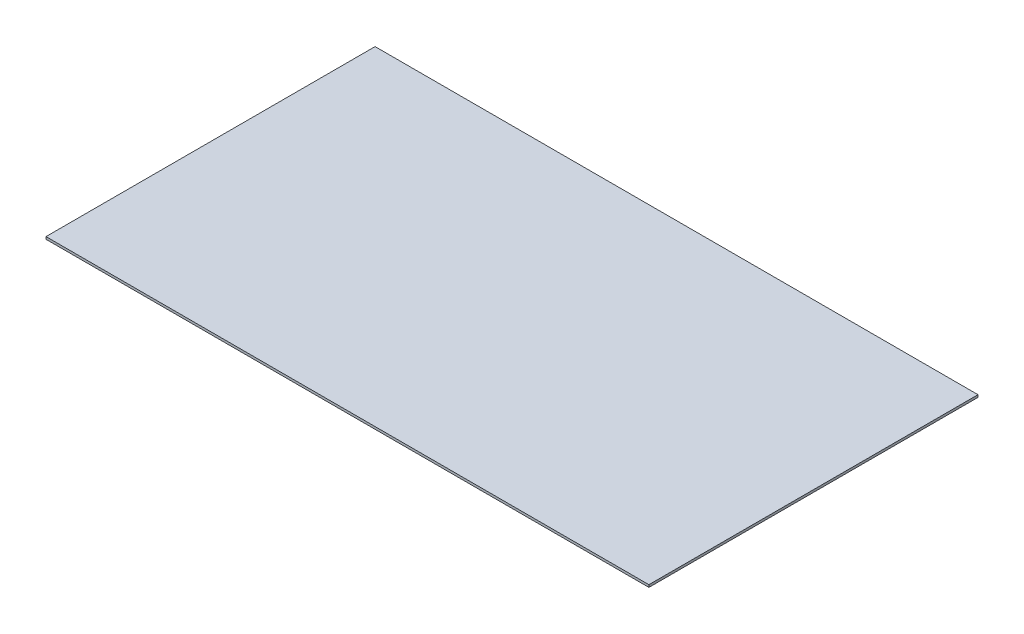
SolidWorks part; units mm, degrees
ref_plane "Front Plane" through (0, 0, 0) normal (0, 0, 1) x (1, 0, 0)
ref_plane "Top Plane" through (0, 0, 0) normal (0, 1, 0) x (1, 0, 0)
ref_plane "Right Plane" through (0, 0, 0) normal (1, 0, 0) x (0, 0, -1)
sketch "Sketch1" plane through (0, 0, 0) normal (0, 1, 0) x (1, 0, 0)
  line L5 (760.349, 415.925) -> (493.649, 415.925) construction
  line L6 (762, 0) -> (762, 419.1) construction
  line L7 (0, 0) -> (762, 0)
  line L8 (0, 0) -> (0, 415.925)
  line L9 (0, 415.925) -> (762, 415.925)
  line L10 (762, 0) -> (762, 415.925)
extrude "Boss-Extrude1" add sketch "Sketch1" along normal blind 3
